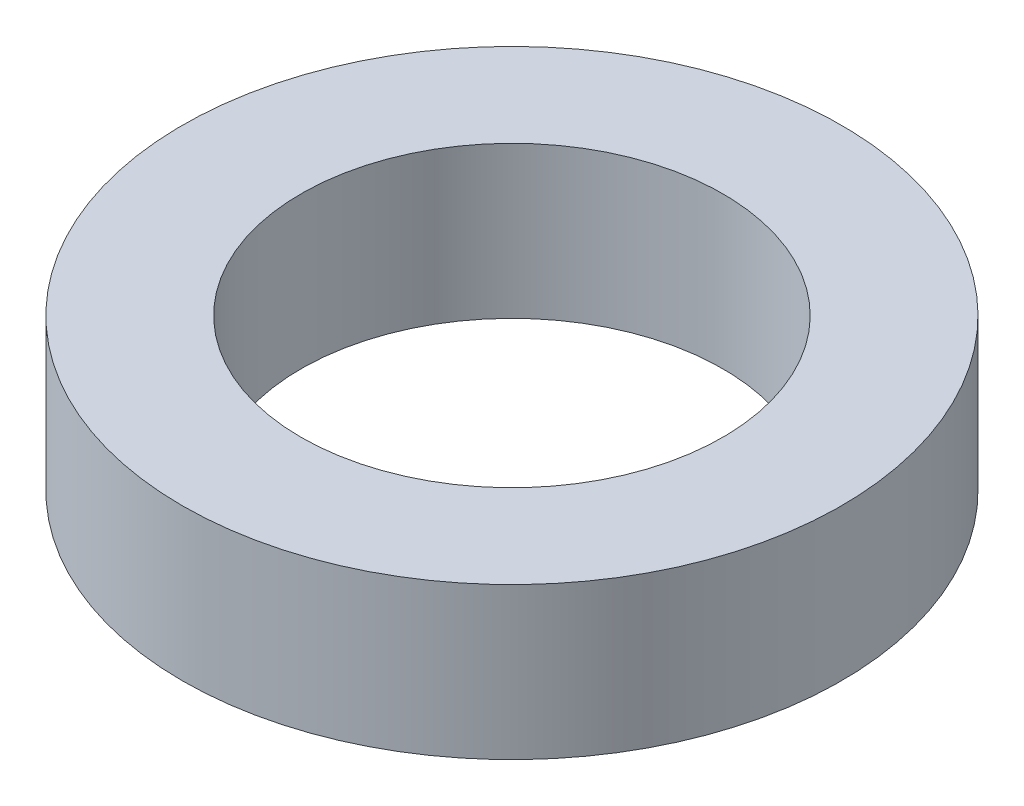
SolidWorks part; units mm, degrees
ref_plane "Płaszczyzna przednia" through (0, 0, 0) normal (0, 0, 1) x (1, 0, 0)
ref_plane "Płaszczyzna górna" through (0, 0, 0) normal (0, 1, 0) x (1, 0, 0)
ref_plane "Płaszczyzna prawa" through (0, 0, 0) normal (1, 0, 0) x (0, 0, -1)
sketch "Sketch1" plane through (0, 0, 0) normal (0, 1, 0) x (1, 0, 0)
  circle A0 centre (0, 0) radius 3.2
  circle A1 centre (0, 0) radius 5
  dimension "D1" = 6.4
  dimension "D2" = 10
extrude "Boss-Extrude1" add sketch "Sketch1" along normal blind 2.3
